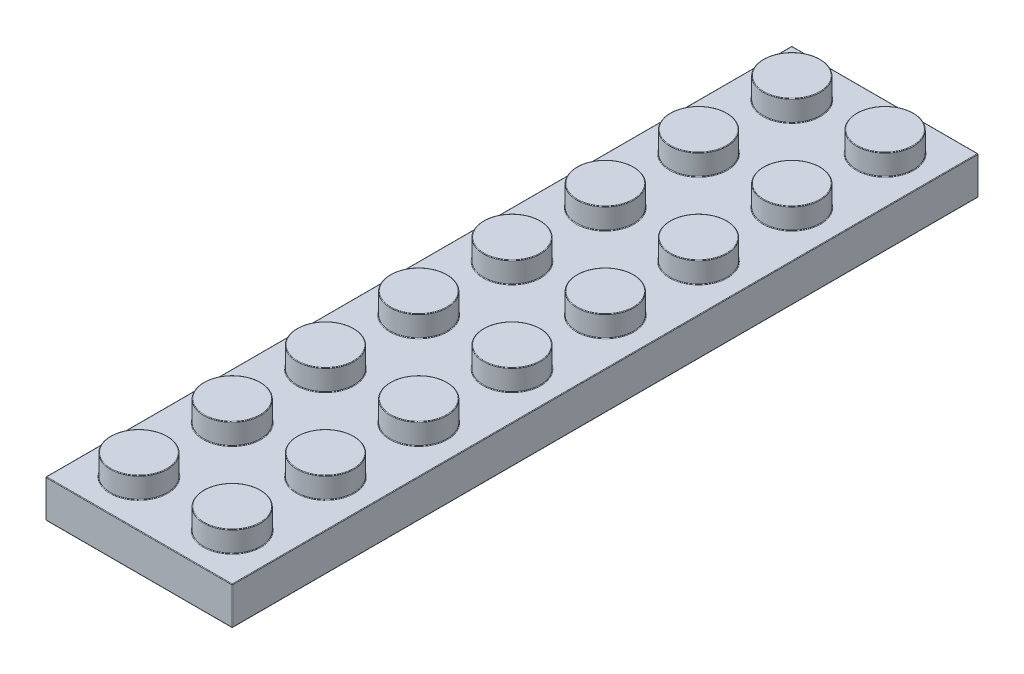
SolidWorks part; units mm, degrees
ref_plane "Front Plane" through (0, 0, 0) normal (0, 0, 1) x (1, 0, 0)
ref_plane "Top Plane" through (0, 0, 0) normal (0, 1, 0) x (1, 0, 0)
ref_plane "Right Plane" through (0, 0, 0) normal (1, 0, 0) x (0, 0, -1)
sketch "Sketch1" plane through (0, 0, 0) normal (0, 1, 0) x (1, 0, 0)
  line L1 (-3.98, 3.98) -> (3.98, 3.98)
  line L2 (-3.98, 3.98) -> (-3.98, -3.98)
  line L3 (-3.98, -3.98) -> (3.98, -3.98)
  line L4 (3.98, 3.98) -> (3.98, -3.98)
  line L5 (-3.98, 3.98) -> (3.98, -3.98) construction
  line L6 (-3.98, -3.98) -> (3.98, 3.98) construction
  point P0 (0, 0)
  dimension "D1" = 7.96
extrude "Extrude1" add sketch "Sketch1" along normal blind 3.22
sketch "Sketch2" plane through (0, 3.22, 0) normal (0, 1, 0) x (1, 0, 0)
  circle A0 centre (0, 0) radius 2.425
  dimension "D1" = 4.85
extrude "Extrude2" add sketch "Sketch2" along normal blind 1.8
pattern_linear "LPattern1" count 2 spacing 7.96 along (-1, 0, 0) of "Extrude2", "Extrude1"
pattern_linear "LPattern2" count 8 spacing 7.96 along (0, 0, -1) of "LPattern1", "Extrude2", "Extrude1"
shell "Shell1" thickness 1.55
sketch "Sketch3" plane through (0, 1.67, 0) normal (0, -1, 0) x (1, 0, 0)
  line L0 (2.43, -58.15) -> (-10.39, -58.15) construction
  line L1 (-10.39, -58.15) -> (-10.39, 2.43) construction
  line L2 (-10.39, 2.43) -> (2.43, 2.43) construction
  line L3 (2.43, 2.43) -> (2.43, -58.15) construction
  line L4 (2.43, -58.15) -> (-10.39, -58.15)
  line L5 (-10.39, -58.15) -> (-10.39, 2.43)
  line L6 (-10.39, 2.43) -> (2.43, 2.43)
  line L7 (2.43, 2.43) -> (2.43, -58.15)
extrude "Extrude3" cut sketch "Sketch3" against normal blind 0.14
sketch "Sketch4" plane through (0, 1.81, 0) normal (0, -1, 0) x (1, 0, 0)
  line L0 (-3.98, 2.43) -> (-3.98, -58.15) construction
  line L1 (2.43, 2.43) -> (-10.39, 2.43) construction
  line L2 (-10.39, -58.15) -> (2.43, -58.15) construction
  line L3 (-3.98, -51.74) -> (-3.98, -43.78) construction
  line L4 (-7.96, -47.76) -> (0, -47.76) construction
  line L5 (-7.96, -47.76) -> (-7.96, -55.72) construction
  line L6 (-7.96, -55.72) -> (0, -55.72) construction
  line L7 (0, -47.76) -> (0, -55.72) construction
  line L8 (-7.96, -47.76) -> (0, -47.76) construction
  line L9 (-7.96, -47.76) -> (-7.96, -39.8) construction
  line L10 (-7.96, -39.8) -> (0, -39.8) construction
  line L11 (0, -47.76) -> (0, -39.8) construction
  line L12 (-7.96, -31.84) -> (0, -31.84) construction
  line L13 (-7.96, -31.84) -> (-7.96, -39.8) construction
  line L14 (-7.96, -39.8) -> (0, -39.8) construction
  line L15 (0, -31.84) -> (0, -39.8) construction
  line L16 (-7.96, -23.88) -> (0, -23.88) construction
  line L17 (-7.96, -23.88) -> (-7.96, -31.84) construction
  line L18 (-7.96, -31.84) -> (0, -31.84) construction
  line L19 (0, -23.88) -> (0, -31.84) construction
  line L20 (-7.96, -15.92) -> (0, -15.92) construction
  line L21 (-7.96, -15.92) -> (-7.96, -23.88) construction
  line L22 (-7.96, -23.88) -> (0, -23.88) construction
  line L23 (0, -15.92) -> (0, -23.88) construction
  line L24 (-7.96, -7.96) -> (0, -7.96) construction
  line L25 (-7.96, -7.96) -> (-7.96, -15.92) construction
  line L26 (-7.96, -15.92) -> (0, -15.92) construction
  line L27 (0, -7.96) -> (0, -15.92) construction
  line L28 (-7.96, 0) -> (0, 0) construction
  line L29 (-7.96, 0) -> (-7.96, -7.96) construction
  line L30 (-7.96, -7.96) -> (0, -7.96) construction
  line L31 (0, 0) -> (0, -7.96) construction
  circle A0 centre (-3.98, -51.74) radius 3.23
  circle A1 centre (-3.98, -51.74) radius 2.37
  circle A2 centre (-3.98, -43.78) radius 3.23
  circle A3 centre (-3.98, -43.78) radius 2.37
  circle A4 centre (-3.98, -35.82) radius 3.23
  circle A5 centre (-3.98, -35.82) radius 2.37
  circle A6 centre (-3.98, -27.86) radius 3.23
  circle A7 centre (-3.98, -27.86) radius 2.37
  circle A8 centre (-3.98, -19.9) radius 3.23
  circle A9 centre (-3.98, -19.9) radius 2.37
  circle A10 centre (-3.98, -11.94) radius 3.23
  circle A11 centre (-3.98, -11.94) radius 2.37
  circle A12 centre (-3.98, -3.98) radius 3.23
  circle A13 centre (-3.98, -3.98) radius 2.37
  point P32 (0, -51.74)
  point P35 (0, -43.78)
  dimension "D1" = 6.46
  dimension "D2" = 0.86
  dimension "D3" = 7.96
extrude "Extrude4" add sketch "Sketch4" along normal up to surface (1.81 mm away) up to face at (-3.98, 0, -27.86)
fillet "Fillet1" radius 0.05 116 edges at (-7.96, 3.22, -21.455) (-7.96, 5.02, -21.455) (-7.96, 3.22, -29.415) (-7.96, 5.02, -29.415) (-3.98, 3.22, 3.98) (0, 3.22, 2.425) (0, 5.02, 2.425) (-7.96, 3.22, -37.375) (-7.96, 5.02, -37.375) (-7.96, 3.22, -45.335) (-7.96, 5.02, -45.335) (-11.94, 1.61, -59.7) (-7.96, 3.22, -53.295) (-7.96, 5.02, -53.295) (-11.94, 0, -27.86) (2.43, 0, -27.86) (2.43, 0.905, 2.43) (-3.98, 0, 2.43) (-10.39, 0.905, 2.43) (0, 3.47, 0.875) (-10.39, 0, -27.86) (-10.39, 0.905, -58.15) (-7.96, 3.47, 0.875) (-3.98, 0, -58.15) (2.43, 0.905, -58.15) (0, 3.47, -7.085) (0, 3.47, -15.045) (0, 3.47, -23.005) (0, 3.47, -30.965) (0, 3.47, -38.925) (0, 3.47, -46.885) (0, 3.47, -54.845) (-7.96, 3.47, -7.085) (-7.96, 3.47, -15.045) (-7.96, 3.47, -23.005) (-7.96, 3.47, -30.965) (-7.96, 3.47, -38.925) (-7.96, 3.47, -46.885) (-7.96, 3.47, -54.845) (-11.94, 1.61, 3.98) (-11.94, 3.22, -27.86) (0, 1.81, 0.875) (-7.96, 1.81, 0.875) (0, 1.81, -7.085) (0, 1.81, -15.045) (0, 1.81, -23.005) (0, 1.81, -30.965) (0, 1.81, -38.925) (0, 1.81, -46.885) (0, 1.81, -54.845) (-7.96, 1.81, -7.085) (-7.96, 1.81, -15.045) (-7.96, 1.81, -23.005) (-7.96, 1.81, -30.965) (-7.96, 1.81, -38.925) (-7.96, 1.81, -46.885) (-7.96, 1.81, -54.845) (2.43, 1.81, -27.86) (-3.98, 1.81, -58.15) (-10.39, 1.81, -27.86) (-3.98, 1.81, 2.43) (-3.98, 1.81, -48.51) (-3.98, 1.81, -54.11) (-3.98, 0, -48.51) (-3.98, 0, -49.37) (-3.98, 1.81, -40.55) (-3.98, 1.81, -46.15) (-3.98, 0, -40.55) (-3.98, 0, -41.41) (-3.98, 1.81, -32.59) (-3.98, 1.81, -38.19) (-3.98, 0, -32.59) (-3.98, 0, -33.45) (-3.98, 1.81, -24.63) (-3.98, 1.81, -30.23) (-3.98, 0, -24.63) (-7.96, 3.22, 2.425) (-3.98, 0, -25.49) (-7.96, 5.02, 2.425) (-3.98, 1.81, -16.67) (-3.98, 1.81, -22.27) (-3.98, 0, -16.67) (-3.98, 0, -17.53) (-3.98, 1.81, -8.71) (-3.98, 1.81, -14.31) (-3.98, 0, -8.71) (-3.98, 0, -9.57) (-3.98, 1.81, -0.75) (-3.98, 1.81, -6.35) (-3.98, 0, -0.75) (-3.98, 0, -1.61) (-3.98, 3.22, -59.7) (-3.98, 0, -59.7) (3.98, 1.61, -59.7) (3.98, 3.22, -27.86) (-3.98, 0, 3.98) (0, 3.22, -5.535) (0, 5.02, -5.535) (0, 3.22, -13.495) (0, 5.02, -13.495) (0, 3.22, -21.455) (0, 5.02, -21.455) (0, 3.22, -29.415) (0, 5.02, -29.415) (0, 3.22, -37.375) (0, 5.02, -37.375) (0, 3.22, -45.335) (0, 5.02, -45.335) (3.98, 0, -27.86) (0, 3.22, -53.295) (0, 5.02, -53.295) (3.98, 1.61, 3.98) (-7.96, 3.22, -5.535) (-7.96, 5.02, -5.535) (-7.96, 3.22, -13.495) (-7.96, 5.02, -13.495)
